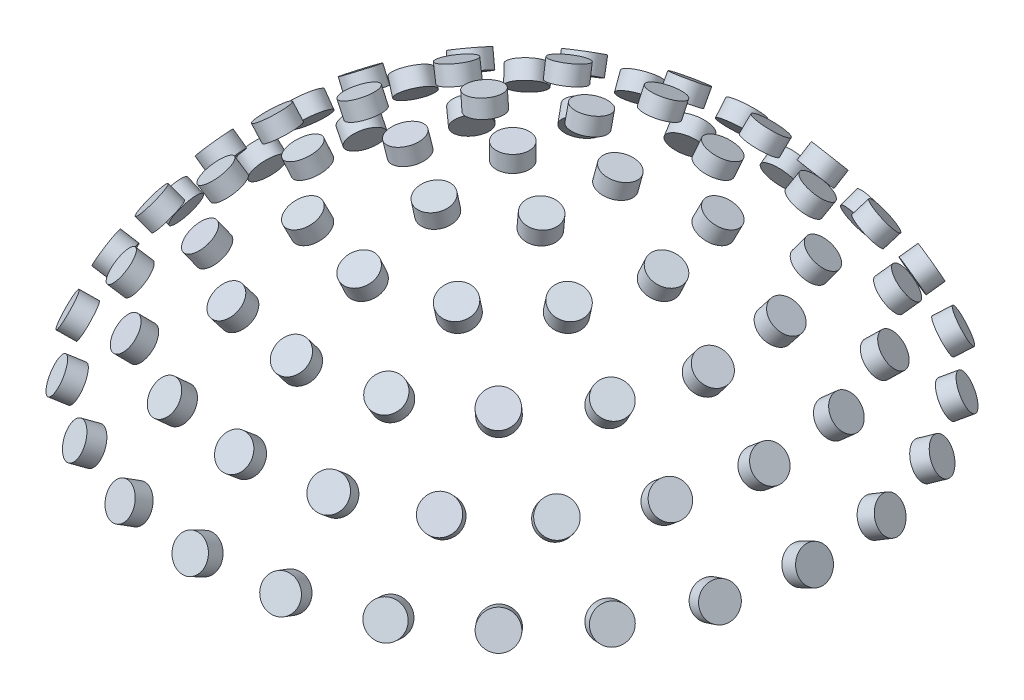
SolidWorks part; units mm, degrees
ref_plane "Front Plane" through (0, 0, 0) normal (0, 0, 1) x (1, 0, 0)
ref_plane "Top Plane" through (0, 0, 0) normal (0, 1, 0) x (1, 0, 0)
ref_plane "Right Plane" through (0, 0, 0) normal (1, 0, 0) x (0, 0, -1)
sketch "Sketch1" plane through (0, 0, 0) normal (0, 0, 1) x (1, 0, 0)
  line L0 (0, 0) -> (10.5, 0)
  line L1 (0, 0) -> (0, 10.5)
  arc A0 (0, 10.5) -> (10.5, 0) centre (0, 0) cw
  dimension "D1" = 10.5
  dimension "D2" = 10.5
ref_plane "Plane1" through (0, 10.5, 0) normal (0, 1, 0) x (1, 0, 0)
sketch "Sketch2" plane through (0, 10.5, 0) normal (0, 1, 0) x (1, 0, 0)
  circle A0 centre (0, 0) radius 0.5
  dimension "D1" = 1
extrude "Boss-Extrude1" add sketch "Sketch2" along normal blind 0.5 contours A0
pattern_circular "CirPattern1" count 2 every 12.5 about axis through (0, 0, 0) along (1, 0, 0) of "Boss-Extrude1"
pattern_circular "CirPattern2" count 2 every 25 about axis through (0, 0, 0) along (1, 0, 0) of bodies 101
pattern_circular "CirPattern3" count 2 every 37.5 about axis through (0, 0, 0) along (1, 0, 0) of bodies 101
pattern_circular "CirPattern4" count 2 every 50 about axis through (0, 0, 0) along (1, 0, 0) of bodies 101
pattern_circular "CirPattern5" count 2 every 62.5 about axis through (0, 0, 0) along (1, 0, 0) of bodies 101
pattern_circular "CirPattern6" count 6 over 360 about axis through (0, 0, 0) along (0, 1, 0) of bodies 102
pattern_circular "CirPattern7" count 12 over 360 about axis through (0, 0, 0) along (0, 1, 0) of bodies 103
pattern_circular "CirPattern8" count 17 over 360 about axis through (0, 0, 0) along (0, 1, 0) of bodies 104
pattern_circular "CirPattern9" count 21 over 360 about axis through (0, 0, 0) along (0, 1, 0) of bodies 105
pattern_circular "CirPattern10" count 25 over 360 about axis through (0, 0, 0) along (0, 1, 0) of bodies 106
sketch "Sketch3" plane through (0, 0, 0) normal (0, 1, 0) x (1, 0, 0)
  circle A0 centre (0, 0) radius 10.5
  dimension "D1" = 21
equation "\"D1@Sketch1\" = \"dia_inner_in\""
equation "\"D2@Sketch1\" = \"dia_inner_in\""
equation "\"D1@Sketch2\"=\"d_marker\""
equation "\"D1@Boss-Extrude1\"=\"t_marker\""
equation "\"D2@CirPattern1\"=\"degrees\""
equation "\"D2@CirPattern2\"=2*\"degrees\""
equation "\"D2@CirPattern3\"=3*\"degrees\""
equation "\"D2@CirPattern4\"=4*\"degrees\""
equation "\"D2@CirPattern5\"=5*\"degrees\""
equation "\"D1@CirPattern6\" = \"n_markers_1\""
equation "\"D1@CirPattern7\" = \"n_markers_2\""
equation "\"D1@CirPattern8\" = \"n_markers_3\""
equation "\"D1@CirPattern9\"= \"n_markers_4\""
equation "\"D1@CirPattern10\" = \"n_markers_5\""
equation "\"dia_difflayer\"= 13"
equation "\"dia_outer_out\"= 12.5"
equation "\"dia_outer_in\"= 12"
equation "\"dia_inner_out\"= 11"
equation "\"dia_inner_in\"= 10.5"
equation "\"degrees\"= 12.5"
equation "\"d_marker\"= 1"
equation "\"t_marker\"= 0.5"
equation "\"n_markers_1\"= 6"
equation "\"n_markers_2\"= round ( 6 * sin ( 2*\"degrees\" ) / sin ( \"degrees\" ) )"
equation "\"n_markers_3\"= round ( 6 * sin ( 3*\"degrees\" ) / sin ( \"degrees\" ) )"
equation "\"n_markers_4\"= round ( 6 * sin ( 4*\"degrees\" ) / sin ( \"degrees\" ) )"
equation "\"n_markers_5\"= round ( 6 * sin ( 5*\"degrees\" ) / sin ( \"degrees\" ) )"
equation "\"n_teeth\"= 8"
